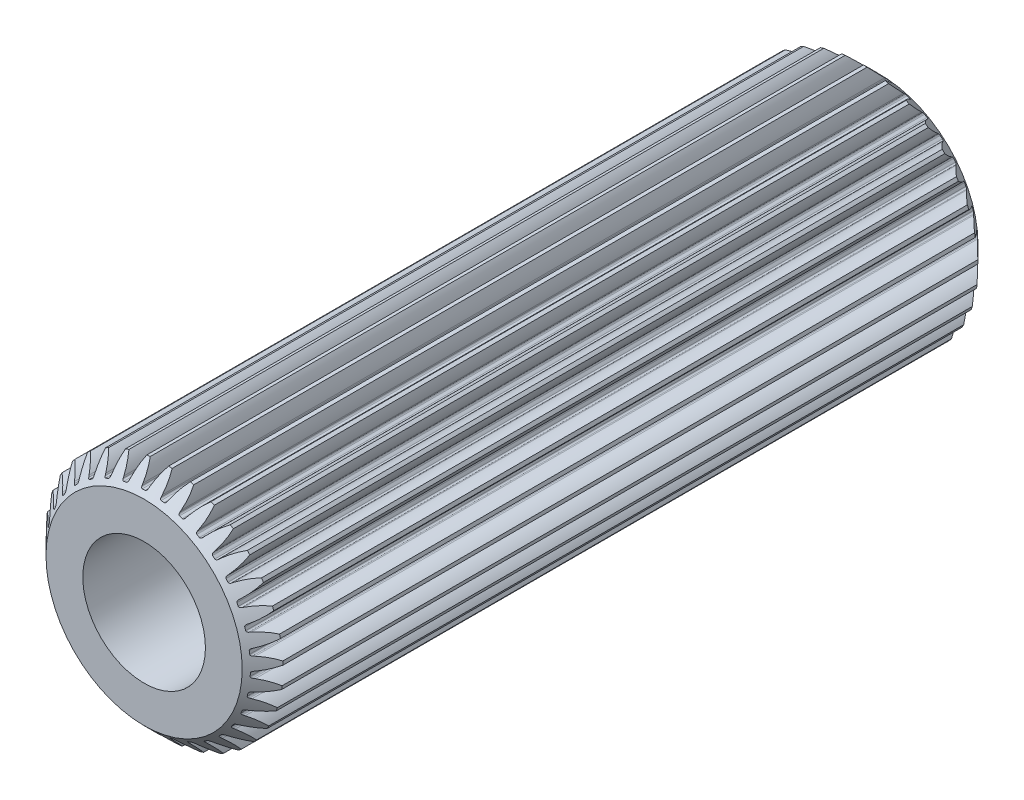
SolidWorks part; units mm, degrees
ref_plane "Piano frontale" through (0, 0, 0) normal (0, 0, 1) x (1, 0, 0)
ref_plane "Piano superiore" through (0, 0, 0) normal (0, 1, 0) x (1, 0, 0)
ref_plane "Piano destro" through (0, 0, 0) normal (1, 0, 0) x (0, 0, -1)
sketch "Schizzo3" plane through (0, 0, 0) normal (0, 0, 1) x (1, 0, 0)
  circle A0 centre (0, 0) radius 2.9
  dimension "D1" = 5.8
extrude "Estrusione-Estrusione2" add sketch "Schizzo3" along normal blind 18
chamfer "Smusso2" distance 0.5 angle 45 2 edges at (2.9, 0, 0) (2.9, 0, 18)
sketch "Schizzo4" plane through (0, 0, 18) normal (0, 0, 1) x (1, 0, 0)
  line L0 (0, 0) -> (2.9, 0) construction
  line L1 (2.73, 0) -> (2.73, -0.9783) construction
  line L2 (2.8731, -0.3942) -> (2.4103, 0.8773) construction
  line L3 (2.5646, -0.0436) -> (2.5318, -0.0491)
  line L4 (0, 0) -> (2.8965, -0.1423) construction
  line L5 (2.5566, -0.208) -> (2.5245, -0.1993)
  circle A0 centre (0, 0) radius 2.9 construction
  arc A1 (2.8769, -0.3653) -> (2.8989, 0.0816) centre (0, 0) ccw
  circle A2 centre (0, 0) radius 2.73 construction
  arc A3 (2.495, -0.1582) -> (2.4985, -0.0871) centre (0, 0) ccw
  circle A4 centre (0, 0) radius 2.565 construction
  arc A5 (2.8989, 0.0816) -> (2.5646, -0.0436) centre (2.4103, 0.8773) cw
  arc A6 (2.8769, -0.3653) -> (2.5566, -0.208) centre (2.3127, -1.1093) ccw
  arc A7 (2.5318, -0.0491) -> (2.4985, -0.0871) centre (2.5385, -0.0885) ccw
  arc A8 (2.5245, -0.1993) -> (2.495, -0.1582) centre (2.5349, -0.1607) cw
  point P22 (2.4994, -0.0545)
  point P25 (2.4927, -0.1907)
  dimension "D1" = 5.46
  dimension "D2" = 5
  dimension "D3" = 5.13
  dimension "D4" = 5.8
  dimension "D7" = 0.04
  dimension "D8" = 0.04
  dimension "D5" = 20
  dimension "D6" = 2.813
extrude "Taglio-Estrusione1" cut sketch "Schizzo4" against normal blind 18
pattern_circular "RipetizioneCircolare1" count 34 over 360 about axis through (0, 0, 0) along (0, 0, 1) of "Taglio-Estrusione1"
sketch "Schizzo6" plane through (0, 0, 18) normal (0, 0, 1) x (1, 0, 0)
  circle A0 centre (0, 0) radius 1.5
  dimension "D1" = 3
extrude "Taglio-Estrusione2" cut sketch "Schizzo6" against normal blind 9
cosmetic thread "Filettatura cosmetica2" parameters "D2"=4
